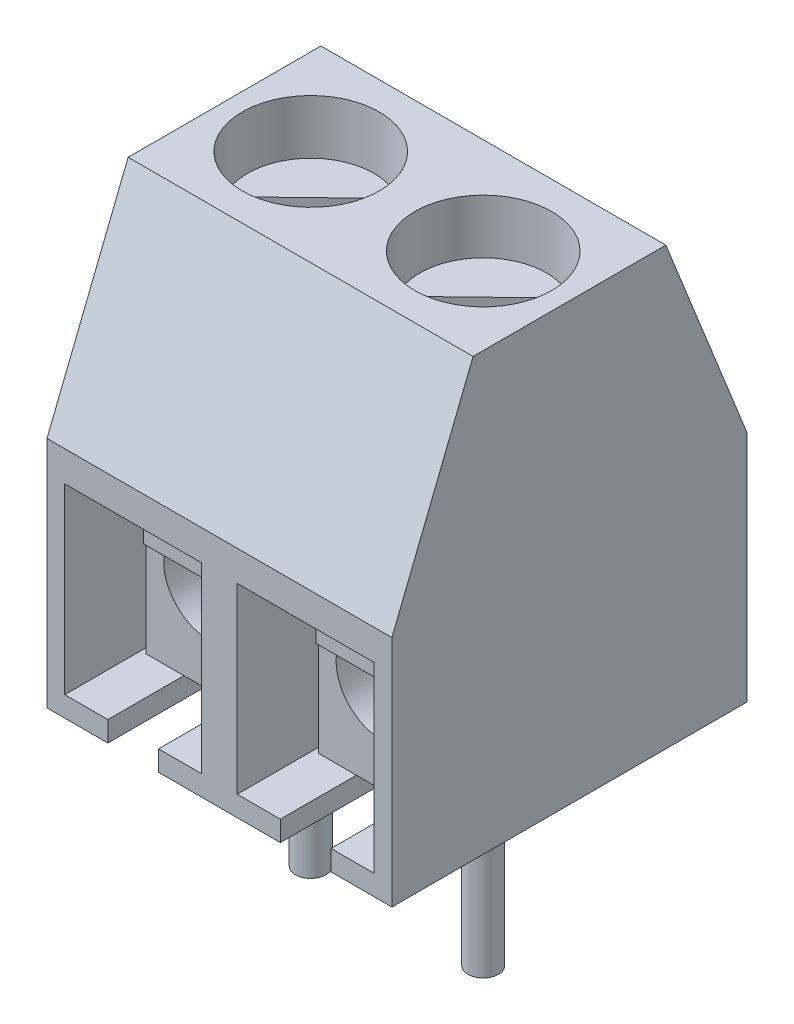
SolidWorks part; units mm, degrees
ref_plane "Plan de face" through (0, 0, 0) normal (0, 0, 1) x (1, 0, 0)
ref_plane "Plan de dessus" through (0, 0, 0) normal (0, 1, 0) x (1, 0, 0)
ref_plane "Plan de droite" through (0, 0, 0) normal (1, 0, 0) x (0, 0, -1)
sketch "Esquisse1" plane through (0, 0, 0) normal (1, 0, 0) x (0, 0, -1)
  line L0 (0, 0) -> (0, 4.6)
  line L1 (0, 4.6) -> (1.6, 8.6)
  line L2 (1.6, 8.6) -> (5.4, 8.6)
  line L3 (7, 4.6) -> (7, 0)
  line L4 (7, 0) -> (0, 0)
  line L5 (5.4, 8.6) -> (7, 4.6)
  line L6 (3.5, 0) -> (3.5, 8.6) construction
  dimension "D1" = 7
  dimension "D2" = 8.6
  dimension "D3" = 3.8
  dimension "D4" = 4
extrude "Boss.-Extru.1" add sketch "Esquisse1" along normal blind 3.4
sketch "Esquisse2" plane through (0, 0, 0) normal (0, 0, 1) x (1, 0, 0)
  line L0 (1.7, 0) -> (1.7, 0.4) construction
  line L1 (0.35, 0.4) -> (1.2, 0.4)
  line L2 (0.35, 0.4) -> (0.35, 4)
  line L3 (0.35, 4) -> (3.05, 4)
  line L4 (3.05, 0.4) -> (3.05, 4)
  line L5 (3.4, 0) -> (0, 0) construction
  line L6 (1.2, 0.4) -> (1.2, 0)
  line L7 (2.2, 0.4) -> (2.2, 0)
  line L8 (2.2, 0.4) -> (3.05, 0.4)
  line L9 (1.2, 0.4) -> (2.2, 0.4) construction
  line L10 (1.2, 0) -> (2.2, 0)
  dimension "D1" = 2.7
  dimension "D2" = 3.6
  dimension "D3" = 0.4
  dimension "D4" = 1
extrude "Enlèv. mat.-Extru.1" cut sketch "Esquisse2" against normal blind 6
sketch "Esquisse3" plane through (0, 8.6, 0) normal (0, 1, 0) x (1, 0, 0)
  line L0 (0, 5.4) -> (3.4, 1.6) construction
  line L1 (3.4, 5.4) -> (0, 1.6) construction
  circle A0 centre (1.7, 3.5) radius 1.35
  dimension "D1" = 2.7
extrude "Enlèv. mat.-Extru.2" cut sketch "Esquisse3" against normal up to next (4.6 mm away)
sketch "Esquisse4" plane through (0, 8.6, 0) normal (0, 1, 0) x (1, 0, 0)
  circle A0 centre (1.7, 3.5) radius 1.25
  dimension "D1" = 2.5
extrude "Boss.-Extru.2" add sketch "Esquisse4" against normal blind 3.4 from offset 1 separate body offset against normal yes
sketch "Esquisse5" plane through (0, 7.6, 0) normal (0, 1, 0) x (1, 0, 0)
  line L0 (0.6187, 2.8729) -> (2.3645, 4.5587)
  line L1 (2.7813, 4.1271) -> (1.0355, 2.4413)
  line L2 (2.3645, 4.5587) -> (1.0355, 2.4413) construction
  line L3 (2.7813, 4.1271) -> (0.6187, 2.8729) construction
  line L4 (1.7, 3.5) -> (1.7, 5.2577) construction
  circle A0 centre (1.7, 3.5) radius 1.25 construction
  arc A1 (0.6187, 2.8729) -> (1.0355, 2.4413) centre (1.7, 3.5) ccw
  arc A2 (2.3645, 4.5587) -> (2.7813, 4.1271) centre (1.7, 3.5) cw
  dimension "D1" = 0.6
  dimension "D2" = 46
extrude "Enlèv. mat.-Extru.3" cut sketch "Esquisse5" against normal blind 0.4
sketch "Esquisse6" plane through (0, 0, 0) normal (0, 0, 1) x (1, 0, 0)
  line L0 (0.35, 0.4) -> (1.2, 0.4) construction
  line L1 (0.45, 0.4) -> (2.95, 0.4)
  line L2 (0.45, 0.4) -> (0.45, 3.9)
  line L3 (0.45, 3.9) -> (0.95, 3.9)
  line L4 (2.95, 0.4) -> (2.95, 3.9)
  line L5 (3.05, 4) -> (0.35, 4) construction
  line L7 (0.45, 3.9) -> (2.95, 0.4) construction
  line L8 (0.95, 3.9) -> (0.95, 3.65)
  line L9 (0.95, 3.65) -> (2.45, 3.65)
  line L10 (2.45, 3.65) -> (2.45, 3.9)
  line L11 (1.7, 2.15) -> (1.7, 4) construction
  line L12 (2.45, 3.9) -> (2.95, 3.9)
  circle A0 centre (1.7, 2.15) radius 0.9
  dimension "D3" = 1.8
  dimension "D1" = 3.5
  dimension "D2" = 2.5
  dimension "D4" = 1.5
  dimension "D5" = 0.25
extrude "Boss.-Extru.3" add sketch "Esquisse6" against normal up to surface (4.5 mm away) from offset 1.5 separate body up to face at (1.7, 1.2, -6) offset against normal yes
sketch "Esquisse7" plane through (0, 0.4, 0) normal (0, -1, 0) x (1, 0, 0)
  line L0 (1.7, -1.5) -> (1.7, -3.5) construction
  line L1 (0.45, -1.5) -> (2.95, -1.5) construction
  line L2 (1.2, 0) -> (0, 0) construction
  circle A0 centre (1.7, -3.5) radius 0.3
  dimension "D1" = 0.6
  dimension "D2" = 3.5
extrude "Boss.-Extru.4" add sketch "Esquisse7" along normal blind 4
ref_plane "Plan1" through (1.7, 0, 0) normal (1, 0, 0) x (0, 0, -1)
sketch "Esquisse8" plane through (1.7, 0, 0) normal (1, 0, 0) x (0, 0, -1)
  line L0 (2.15, 3.8) -> (1.5, 3.8)
  line L1 (1, 3.3) -> (1, 2.9)
  line L2 (1, 2.9) -> (2.4555, 1.6787)
  line L3 (2.15, 8.6) -> (2.15, 4) construction
  line L4 (6, 3.65) -> (1.5, 3.65) construction
  line L5 (1.5, 0.4) -> (1.5, 3.9) construction
  arc A0 (1.5, 3.8) -> (1, 3.3) centre (1.5, 3.3) ccw
  dimension "D2" = 0.5
  dimension "D1" = 0.15
  dimension "D3" = 0.4
  dimension "D4" = 1.9
  dimension "D5" = 130
extrude "Extru.-Mince1" add sketch "Esquisse8" along normal mid plane 1.4 separate body thin thin type mid plane wall 0.2
pattern_linear "Répétition linéaire2" count 2 spacing 3.4 along (1, 0, 0) of "Boss.-Extru.1", "Enlèv. mat.-Extru.2", "Enlèv. mat.-Extru.1"
pattern_linear "Répétition linéaire3" count 2 spacing 3.4 along (1, 0, 0) of bodies 105 108 107
